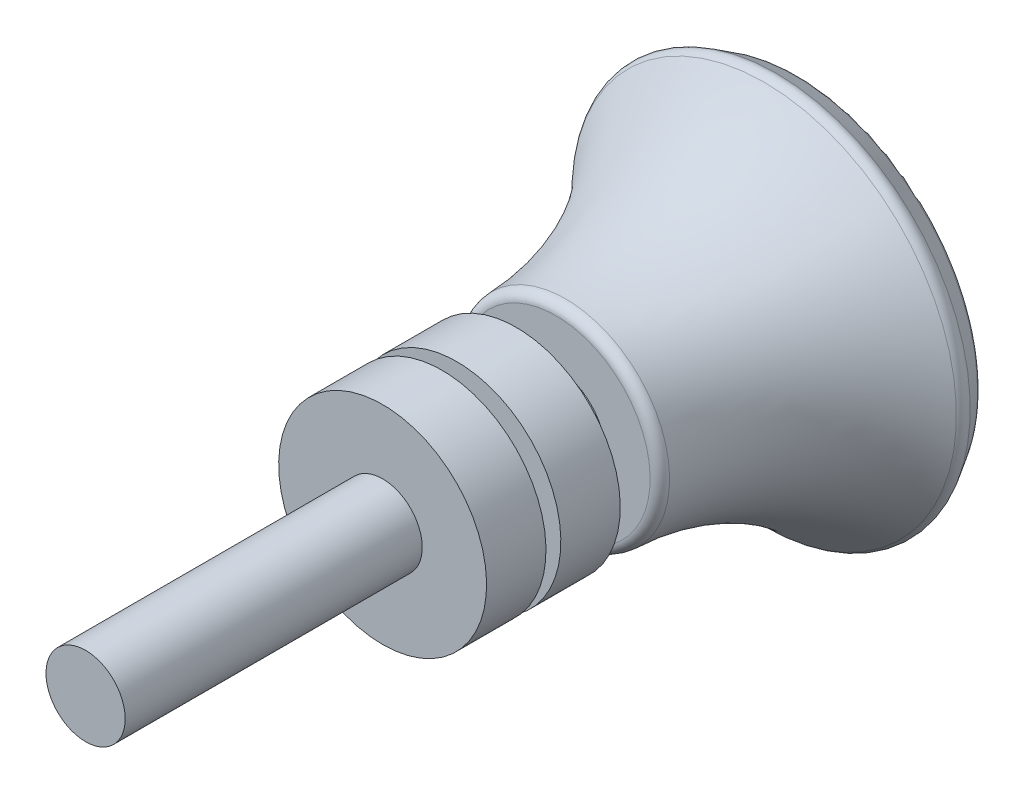
SolidWorks part; units mm, degrees
ref_plane "Спереди" through (0, 0, 0) normal (0, 0, 1) x (1, 0, 0)
ref_plane "Сверху" through (0, 0, 0) normal (0, 1, 0) x (1, 0, 0)
ref_plane "Справа" through (0, 0, 0) normal (1, 0, 0) x (0, 0, -1)
sketch "Эскиз1" plane through (0, 0, 0) normal (1, 0, 0) x (0, 0, -1)
  line L0 (-37.5, 0) -> (-37.5, 4)
  line L1 (-37.5, 4) -> (-7.5, 4)
  line L2 (-7.5, 4) -> (-7.5, 10.5)
  line L3 (-7.5, 10.5) -> (-1.5, 10.5)
  line L4 (-1.5, 10.5) -> (-1.5, 5)
  line L5 (-1.5, 5) -> (0, 5)
  line L6 (0, 5) -> (0, 10.5)
  line L7 (0, 10.5) -> (6, 10.5)
  line L8 (6, 10.5) -> (6, 5)
  line L9 (6, 5) -> (10, 5)
  line L10 (10, 5) -> (10, 9.5165)
  line L11 (-37.5, 0) -> (30, 0)
  line L12 (32.269, 19.5817) -> (34.1563, 18.4403)
  line L14 (-37.5, 0) -> (30, 0) construction
  arc A0 (10.9669, 10.516) -> (31.0325, 19.421) centre (10, 39.754) ccw
  arc A1 (34.5087, 17.0913) -> (30, 0) centre (64.6488, 0) ccw
  arc A2 (31.0325, 19.421) -> (32.269, 19.5817) centre (31.7515, 18.726) cw
  arc A3 (34.1563, 18.4403) -> (34.5087, 17.0913) centre (33.6388, 17.5846) cw
  arc A4 (10, 9.5165) -> (10.9669, 10.516) centre (11, 9.5165) cw
  point P14 (-4.5, 10.5)
  point P18 (0, 0)
  point P21 (31.5772, 20)
  point P25 (35, 17.9301)
  point P28 (10, 10.5)
  dimension "D11" = 1
  dimension "D12" = 1
  dimension "D13" = 1
  dimension "D1" = 10
  dimension "D2" = 8
  dimension "D3" = 6
  dimension "D4" = 1.5
  dimension "D5" = 21
  dimension "D6" = 20
  dimension "D7" = 4
  dimension "D8" = 5
  dimension "D9" = 40
  dimension "D10" = 4
  dimension "D14" = 30
revolve "Повернуть1" add sketch "Эскиз1" angle 360 about L14
